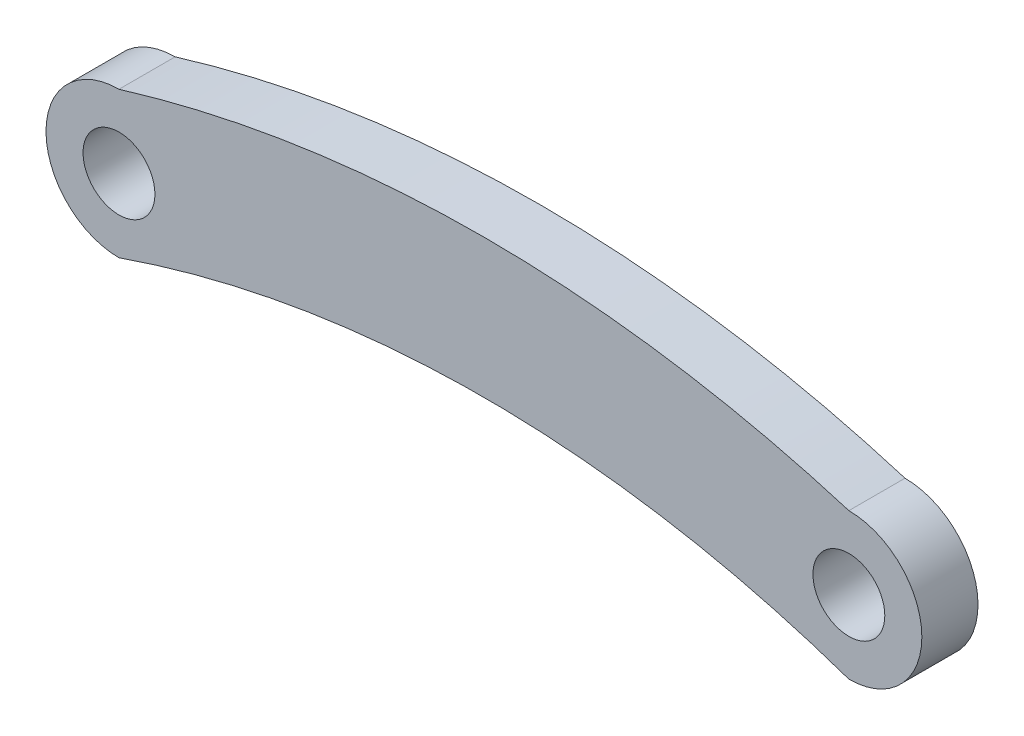
SolidWorks part; units mm, degrees
ref_plane "Front Plane" through (0, 0, 0) normal (0, 0, 1) x (1, 0, 0)
ref_plane "Top Plane" through (0, 0, 0) normal (0, 1, 0) x (1, 0, 0)
ref_plane "Right Plane" through (0, 0, 0) normal (1, 0, 0) x (0, 0, -1)
sketch "Sketch1" plane through (0, 0, 0) normal (0, 0, 1) x (1, 0, 0)
  line L0 (-32.5, 0) -> (0, 0) construction
  line L3 (-16.25, 0) -> (-16.25, -50) construction
  arc A0 (-32.5, 3.25) -> (-32.5, -3.25) centre (-32.5, 0) ccw
  arc A1 (0, -3.25) -> (0, 3.25) centre (0, 0) ccw
  circle A2 centre (-32.5, 0) radius 1.6
  circle A3 centre (0, 0) radius 1.6
  arc A4 (-32.5, 3.25) -> (0, 3.25) centre (-16.25, -50) cw
  arc A5 (-32.5, -3.25) -> (0, -3.25) centre (-16.25, -50) cw
  point P2 (-16.25, 0)
  dimension "D1" = 3.25
  dimension "D3" = 3.2
  dimension "D2" = 32.5
  dimension "D4" = 50
extrude "Boss-Extrude1" add sketch "Sketch1" along normal blind 2.5
